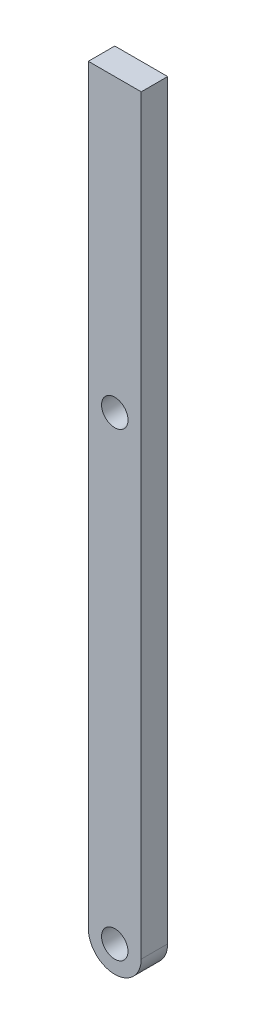
SolidWorks part; units mm, degrees
ref_plane "Front Plane" through (0, 0, 0) normal (0, 0, 1) x (1, 0, 0)
ref_plane "Top Plane" through (0, 0, 0) normal (0, 1, 0) x (1, 0, 0)
ref_plane "Right Plane" through (0, 0, 0) normal (1, 0, 0) x (0, 0, -1)
sketch "Sketch1" plane through (0, 0, 0) normal (0, 0, 1) x (1, 0, 0)
  line L0 (0, 0) -> (0, 110.49) construction
  line L1 (-6.35, 110.49) -> (-6.35, 0)
  line L2 (6.35, 110.49) -> (6.35, 0)
  line L5 (-6.35, 110.49) -> (-6.35, 180.34)
  line L6 (-6.35, 180.34) -> (6.35, 180.34)
  line L7 (6.35, 110.49) -> (6.35, 180.34)
  arc A0 (-6.35, 0) -> (6.35, 0) centre (0, 0) ccw
  circle A2 centre (0, 110.49) radius 3.175
  circle A3 centre (0, 0) radius 3.175
  point P12 (6.35, 180.34)
  point P13 (-6.35, 180.34)
  dimension "D1" = 6.35
  dimension "4.35" = 110.49
  dimension "D3" = 69.85
extrude "Boss-Extrude1" add sketch "Sketch1" along normal blind 6.35
